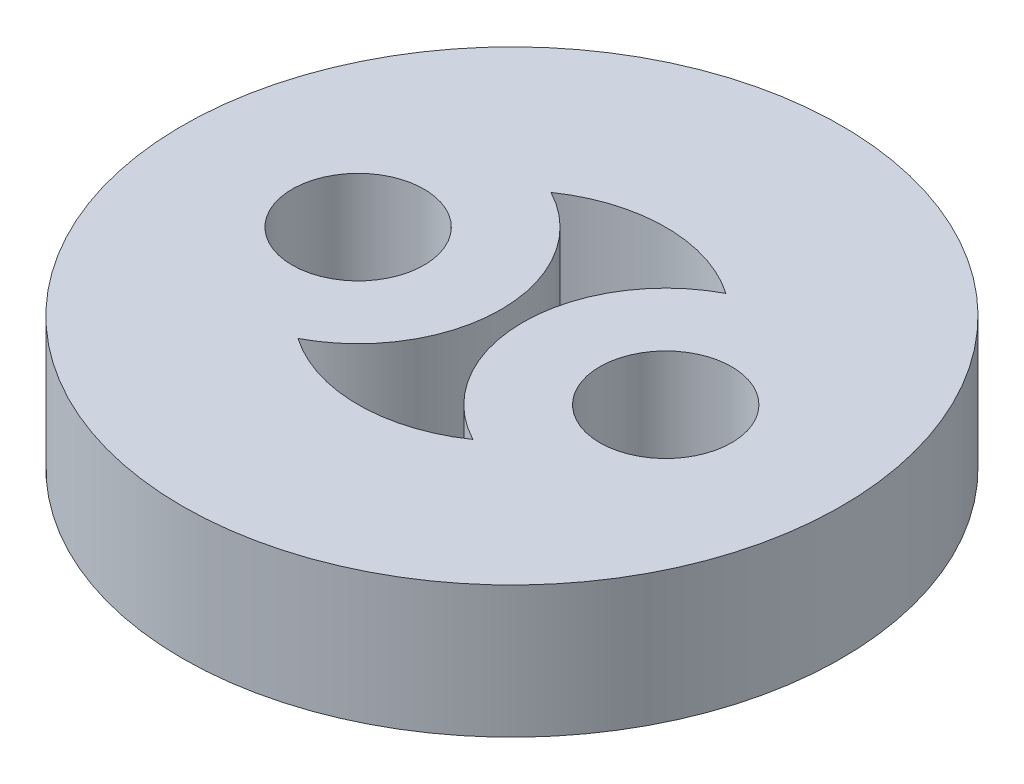
SolidWorks part; units mm, degrees
ref_plane "Plan de face" through (0, 0, 0) normal (0, 0, 1) x (1, 0, 0)
ref_plane "Plan de dessus" through (0, 0, 0) normal (0, 1, 0) x (1, 0, 0)
ref_plane "Plan de droite" through (0, 0, 0) normal (1, 0, 0) x (0, 0, -1)
sketch "Esquisse1" plane through (0, 0, 0) normal (0, 1, 0) x (1, 0, 0)
  line L0 (-3.5, 0) -> (3.5, 0) construction
  circle A0 centre (0, 0) radius 7.5
  circle A2 centre (-3.5, 0) radius 1.5
  circle A3 centre (3.5, 0) radius 1.5
  arc A4 (1.9911, 2.8785) -> (1.9911, -2.8785) centre (3.5, 0) ccw
  arc A5 (-1.9911, -2.8785) -> (-1.9911, 2.8785) centre (-3.5, 0) ccw
  arc A6 (-1.9911, -2.8785) -> (1.9911, -2.8785) centre (0, 0) ccw
  arc A9 (1.9911, 2.8785) -> (-1.9911, 2.8785) centre (0, 0) ccw
  circle A10 centre (-3.5, 0) radius 3.25 construction
  circle A11 centre (3.5, 0) radius 3.25 construction
  dimension "D1" = 15
  dimension "D2" = 6.5
  dimension "D3" = 6.5
  dimension "D4" = 7
  dimension "D5" = 3
  dimension "D6" = 3
  dimension "D7" = 3.5
  dimension "D8" = 3.5
  dimension "D9" = 3.25
  dimension "D10" = 3.25
  dimension "D11" = 3.5
extrude "Boss.-Extru.1" add sketch "Esquisse1" along normal blind 3
